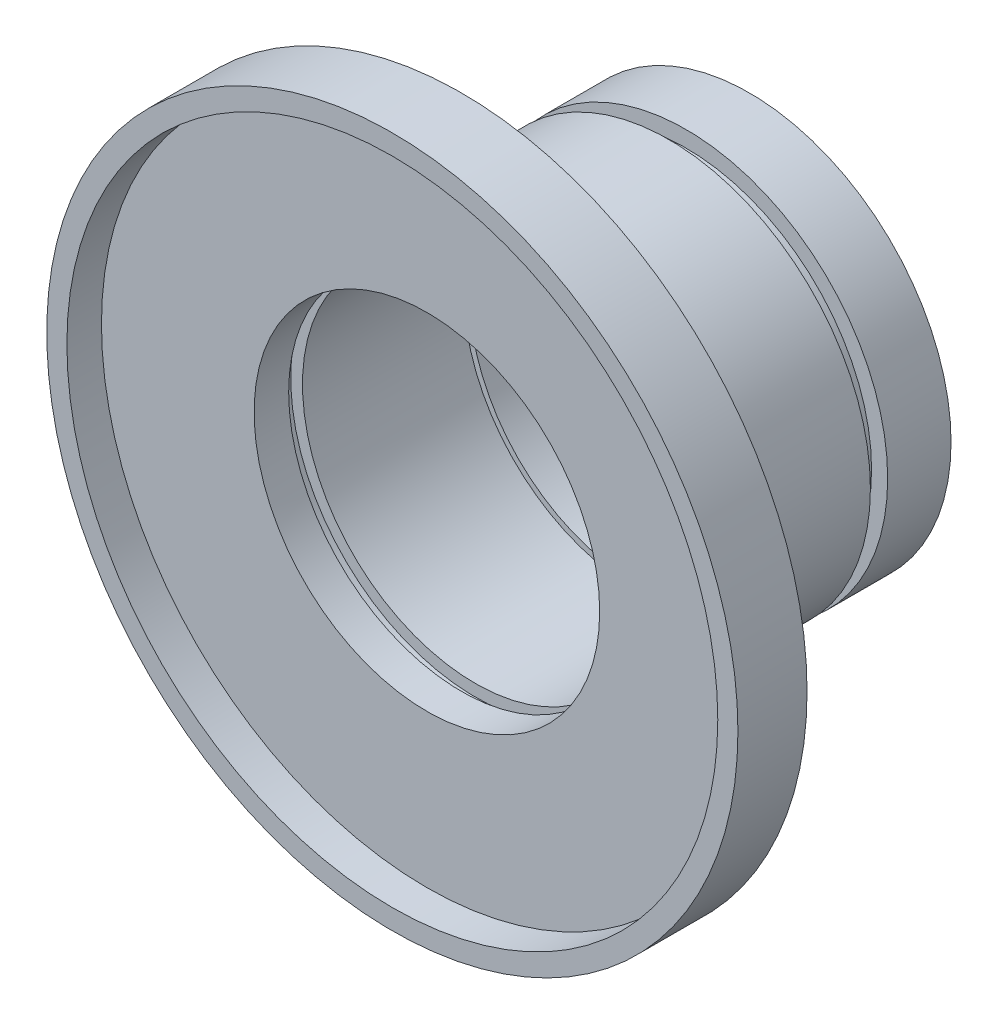
SolidWorks part; units mm, degrees
ref_plane "前视基准面" through (0, 0, 0) normal (0, 0, 1) x (1, 0, 0)
ref_plane "上视基准面" through (0, 0, 0) normal (0, 1, 0) x (1, 0, 0)
ref_plane "右视基准面" through (0, 0, 0) normal (1, 0, 0) x (0, 0, -1)
sketch "草图1" plane through (0, 0, 0) normal (0, 0, 1) x (1, 0, 0)
  circle A0 centre (0, 0) radius 30
  circle A1 centre (0, 0) radius 28.251
extrude "凸台-拉伸1" add sketch "草图1" along normal blind 3
sketch "草图2" plane through (0, 0, 0) normal (0, 0, 1) x (1, 0, 0)
  circle A0 centre (0, 0) radius 30
  circle A1 centre (0, 0) radius 15
extrude "凸台-拉伸2" add sketch "草图2" against normal blind 3
ref_plane "基准面1" through (0, 0, -3) normal (0, 0, -1) x (-1, 0, 0)
sketch "草图4" plane through (0, 0, -3) normal (0, 0, -1) x (-1, 0, 0)
  circle A0 centre (0, 0) radius 15
  circle A1 centre (0, 0) radius 17.5
extrude "凸台-拉伸3" add sketch "草图4" along normal blind 20
ref_plane "基准面2" through (0, 0, -23) normal (0, 0, -1) x (-1, 0, 0)
sketch "草图5" plane through (0, 0, -23) normal (0, 0, -1) x (-1, 0, 0)
  circle A0 centre (0, 0) radius 14.5
  circle A1 centre (0, 0) radius 17.5
extrude "凸台-拉伸4" add sketch "草图5" along normal blind 0.5
sketch "草图6" plane through (0, 0, 0) normal (1, 0, 0) x (0, 0, -1)
  line L0 (-3, 0) -> (25, 0) construction
  line L1 (21, 17.5) -> (22.5, 17.5)
  line L2 (22.5, 17.5) -> (22.5, 16.1)
  line L3 (22.5, 16.1) -> (21, 16.1)
  line L4 (21, 16.1) -> (21, 17.5)
revolve "切除-旋转1" cut sketch "草图6" angle 360 about L0
sketch "草图7" plane through (0, 0, 0) normal (1, 0, 0) x (0, 0, -1)
  line L0 (-3, 0) -> (25, 0) construction
  line L1 (3, 16.0236) -> (3, 14.9736)
  line L2 (3, 16.0236) -> (4.2, 16.0236)
  line L3 (4.2, 16.0236) -> (4.2, 14.9736)
  line L5 (4.2, 14.9736) -> (3, 14.9736)
revolve "切除-旋转2" cut sketch "草图7" angle 360 about L0
sketch "草图8" plane through (0, 0, -23) normal (0, 0, -1) x (-1, 0, 0)
  circle A0 centre (0, 0) radius 15
  circle A1 centre (0, 0) radius 14.5
extrude "凸台-拉伸5" add sketch "草图8" against normal blind 4.8
ref_plane "基准面3" through (0, 0, -23.5) normal (0, 0, -1) x (-1, 0, 0)
sketch "草图9" plane through (0, 0, -23.5) normal (0, 0, -1) x (-1, 0, 0)
  circle A0 centre (0, 0) radius 17.5
  circle A1 centre (0, 0) radius 11.5
extrude "凸台-拉伸6" add sketch "草图9" along normal blind 4.5
ref_plane "基准面4" through (0, 0, -28) normal (0, 0, -1) x (-1, 0, 0)
sketch "草图10" plane through (0, 0, -28) normal (0, 0, -1) x (-1, 0, 0)
  line L0 (0, -15.5) -> (0, 15.5) construction
  line L1 (15.5, 0) -> (-15.5, 0) construction
  line L2 (5.451, 12.4413) -> (4.4018, 10.6242)
  line L3 (8.049, 10.9413) -> (6.9999, 9.1242)
  line L4 (5.451, 12.4413) -> (6.4146, 14.1104)
  line L5 (-1.5, 13.5) -> (-1.5, 11.4018)
  line L6 (1.5, 13.5) -> (1.5, 11.4018)
  line L7 (-1.5, 13.5) -> (-1.5, 15.4272)
  line L8 (1.5, 13.5) -> (1.5, 15.4272)
  line L9 (8.049, 10.9413) -> (9.0127, 12.6104)
  line L10 (-7.75, -13.4234) -> (7.75, 13.4234) construction
  line L11 (10.9413, 8.049) -> (9.1242, 6.9999)
  line L12 (12.4413, 5.451) -> (10.6242, 4.4018)
  line L13 (10.9413, 8.049) -> (12.6104, 9.0127)
  line L14 (12.4413, 5.451) -> (14.1104, 6.4146)
  line L15 (-13.4234, -7.75) -> (13.4234, 7.75) construction
  line L16 (13.5, 1.5) -> (11.4018, 1.5)
  line L17 (13.5, -1.5) -> (11.4018, -1.5)
  line L18 (13.5, 1.5) -> (15.4272, 1.5)
  line L19 (13.5, -1.5) -> (15.4272, -1.5)
  line L20 (-15.5, 0) -> (15.5, 0) construction
  line L21 (12.4413, -5.451) -> (10.6242, -4.4018)
  line L22 (10.9413, -8.049) -> (9.1242, -6.9999)
  line L23 (12.4413, -5.451) -> (14.1104, -6.4146)
  line L24 (10.9413, -8.049) -> (12.6104, -9.0127)
  line L25 (-13.4234, 7.75) -> (13.4234, -7.75) construction
  line L26 (8.049, -10.9413) -> (6.9999, -9.1242)
  line L27 (5.451, -12.4413) -> (4.4018, -10.6242)
  line L28 (8.049, -10.9413) -> (9.0127, -12.6104)
  line L29 (5.451, -12.4413) -> (6.4146, -14.1104)
  line L30 (-7.75, 13.4234) -> (7.75, -13.4234) construction
  line L31 (1.5, -13.5) -> (1.5, -11.4018)
  line L32 (-1.5, -13.5) -> (-1.5, -11.4018)
  line L33 (1.5, -13.5) -> (1.5, -15.4272)
  line L34 (-1.5, -13.5) -> (-1.5, -15.4272)
  line L35 (0, 15.5) -> (0, -15.5) construction
  line L36 (-5.451, -12.4413) -> (-4.4018, -10.6242)
  line L37 (-8.049, -10.9413) -> (-6.9999, -9.1242)
  line L38 (-5.451, -12.4413) -> (-6.4146, -14.1104)
  line L39 (-8.049, -10.9413) -> (-9.0127, -12.6104)
  line L40 (7.75, 13.4234) -> (-7.75, -13.4234) construction
  line L41 (-10.9413, -8.049) -> (-9.1242, -6.9999)
  line L42 (-12.4413, -5.451) -> (-10.6242, -4.4018)
  line L43 (-10.9413, -8.049) -> (-12.6104, -9.0127)
  line L44 (-12.4413, -5.451) -> (-14.1104, -6.4146)
  line L45 (13.4234, 7.75) -> (-13.4234, -7.75) construction
  line L46 (-13.5, -1.5) -> (-11.4018, -1.5)
  line L47 (-13.5, 1.5) -> (-11.4018, 1.5)
  line L48 (-13.5, -1.5) -> (-15.4272, -1.5)
  line L49 (-13.5, 1.5) -> (-15.4272, 1.5)
  line L50 (15.5, 0) -> (-15.5, 0) construction
  line L51 (-12.4413, 5.451) -> (-10.6242, 4.4018)
  line L52 (-10.9413, 8.049) -> (-9.1242, 6.9999)
  line L53 (-12.4413, 5.451) -> (-14.1104, 6.4146)
  line L54 (-10.9413, 8.049) -> (-12.6104, 9.0127)
  line L55 (13.4234, -7.75) -> (-13.4234, 7.75) construction
  line L56 (-8.049, 10.9413) -> (-6.9999, 9.1242)
  line L57 (-5.451, 12.4413) -> (-4.4018, 10.6242)
  line L58 (-8.049, 10.9413) -> (-9.0127, 12.6104)
  line L59 (-5.451, 12.4413) -> (-6.4146, 14.1104)
  line L60 (7.75, -13.4234) -> (-7.75, 13.4234) construction
  circle A0 centre (0, 0) radius 11.5
  circle A1 centre (0, 0) radius 15.5
  point P104 (0, 0)
  dimension "D1" = 12
extrude "切除-拉伸1" cut sketch "草图10" against normal blind 5 contours L8 A1 L7 L5 A0 L6 | L9 A1 L4 L2 A0 L3 | L14 A1 L13 L11 A0 L12 | L19 A1 L18 L16 A0 L17 | L24 A1 L23 L21 A0 L22 | L29 A1 L28 L26 A0 L27 | L34 A1 L33 L31 A0 L32 | L39 A1 L38 L36 A0 L37 | L44 A1 L43 L41 A0 L42 | L49 A1 L48 L46 A0 L47 | L54 A1 L53 L51 A0 L52 | L59 A1 L58 L56 A0 L57
